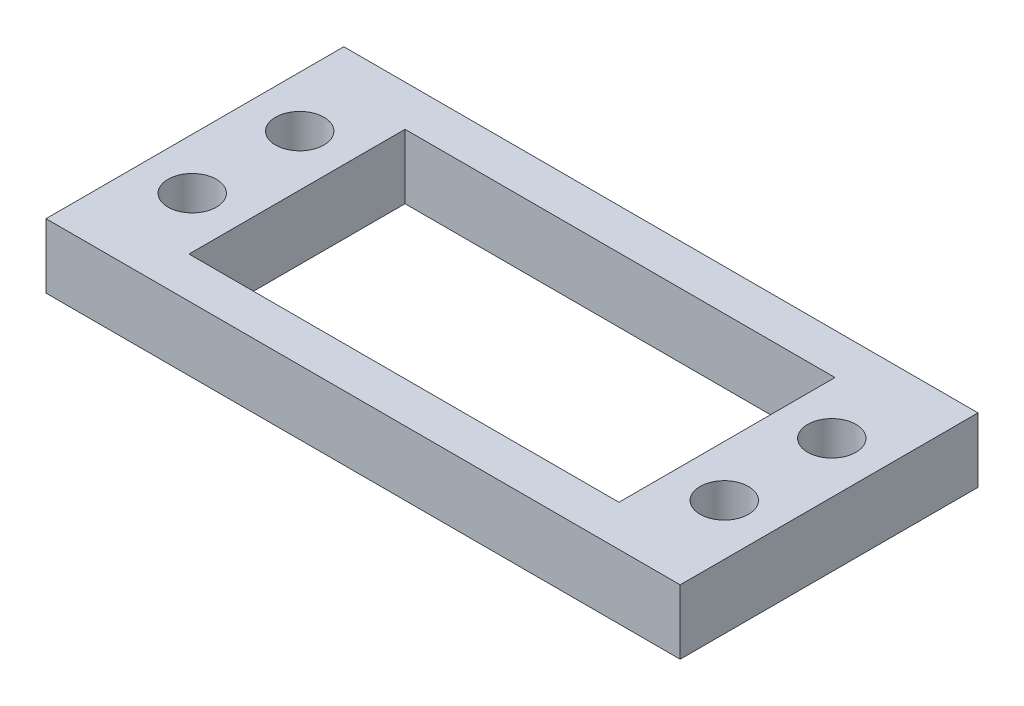
SolidWorks part; units mm, degrees
ref_plane "Front Plane" through (0, 0, 0) normal (0, 0, 1) x (1, 0, 0)
ref_plane "Top Plane" through (0, 0, 0) normal (0, 1, 0) x (1, 0, 0)
ref_plane "Right Plane" through (0, 0, 0) normal (1, 0, 0) x (0, 0, -1)
sketch "Sketch1" plane through (0, 0, 0) normal (0, 1, 0) x (1, 0, 0)
  line L0 (49.5, 8.8536) -> (59, 8.8536) construction
  line L1 (0, 0) -> (59, 0)
  line L2 (0, 0) -> (0, 27.7073)
  line L3 (0, 27.7073) -> (59, 27.7073)
  line L4 (59, 0) -> (59, 27.7073)
  line L5 (0, 0) -> (59, 27.7073) construction
  line L6 (0, 27.7073) -> (59, 0) construction
  line L7 (4.75, 8.8536) -> (54.25, 8.8536) construction
  line L8 (4.75, 8.8536) -> (4.75, 18.8536) construction
  line L9 (4.75, 18.8536) -> (54.25, 18.8536) construction
  line L10 (54.25, 8.8536) -> (54.25, 18.8536) construction
  line L11 (4.75, 8.8536) -> (54.25, 18.8536) construction
  line L12 (4.75, 18.8536) -> (54.25, 8.8536) construction
  line L15 (52.472, 27.7073) -> (59, 27.7073) construction
  line L16 (59, 13.9934) -> (59, 27.7073) construction
  line L19 (9.5, 3.8036) -> (49.5, 3.8036)
  line L20 (9.5, 3.8036) -> (9.5, 23.9036)
  line L21 (9.5, 23.9036) -> (49.5, 23.9036)
  line L22 (49.5, 3.8036) -> (49.5, 23.9036)
  line L23 (9.5, 3.8036) -> (49.5, 23.9036) construction
  line L24 (9.5, 23.9036) -> (49.5, 3.8036) construction
  circle A0 centre (4.75, 18.8536) radius 2.25
  circle A1 centre (4.75, 8.8536) radius 2.25
  circle A2 centre (54.25, 8.8536) radius 2.25
  circle A3 centre (54.25, 18.8536) radius 2.25
  point P4 (29.5, 13.8536)
  point P6 (29.5, 13.8536)
  point P14 (29.5, 13.8536)
  point P25 (54.25, 8.8536)
  dimension "D3" = 4.5
  dimension "D1" = 49.5
  dimension "D2" = 10
  dimension "D4" = 20.1
  dimension "D5" = 40
extrude "Boss-Extrude1" add sketch "Sketch1" along normal blind 6
